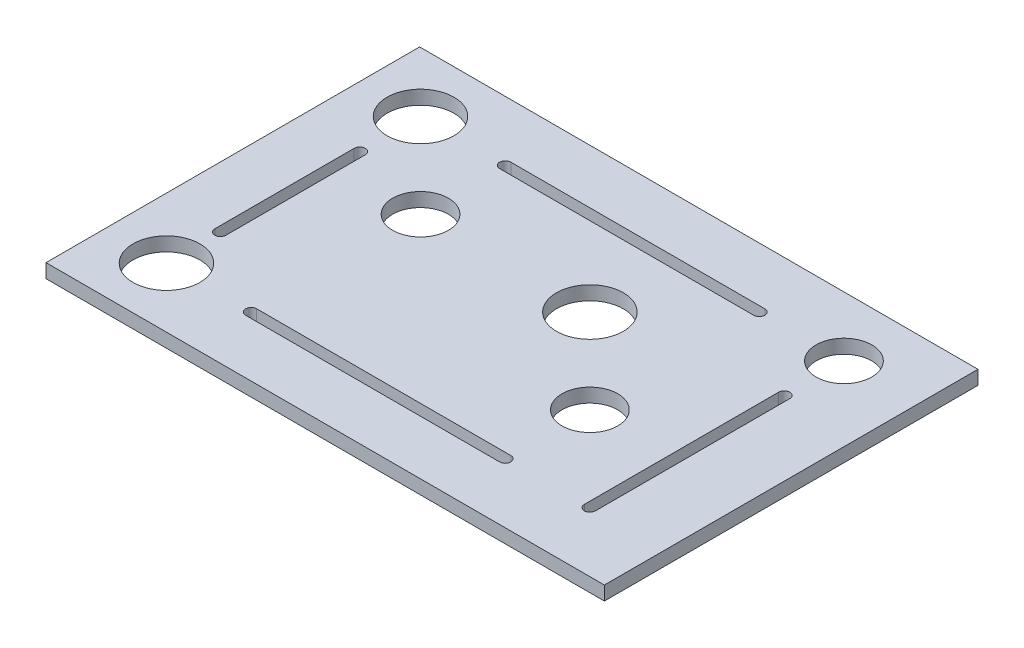
SolidWorks part; units mm, degrees
ref_plane "Front Plane" through (0, 0, 0) normal (0, 0, 1) x (1, 0, 0)
ref_plane "Top Plane" through (0, 0, 0) normal (0, 1, 0) x (1, 0, 0)
ref_plane "Right Plane" through (0, 0, 0) normal (1, 0, 0) x (0, 0, -1)
sketch "Sketch1" plane through (0, 0, 0) normal (0, 1, 0) x (1, 0, 0)
  line L1 (0, 0) -> (-127.25, 0)
  line L2 (0, 0) -> (0, 85.15)
  line L3 (0, 85.15) -> (-127.25, 85.15)
  line L4 (-127.25, 0) -> (-127.25, 85.15)
  dimension "D1" = 85.15
  dimension "D2" = 127.25
extrude "Boss-Extrude1" add sketch "Sketch1" along normal blind 3.175 contours L4 L3 L2 L1
sketch "Sketch2" plane through (0, 3.175, 0) normal (0, 1, 0) x (1, 0, 0)
  circle A0 centre (-16.925, 71.525) radius 6.35
  dimension "D1" = 12.7
extrude "Cut-Extrude1" cut sketch "Sketch2" against normal through all
sketch "Sketch3" plane through (0, 0, 0) normal (0, -1, 0) x (-1, 0, 0)
  circle A0 centre (113.425, 71.525) radius 7.62
  circle A1 centre (113.425, 13.625) radius 7.62
  circle A2 centre (94.125, 52.225) radius 6.35
  circle A3 centre (55.525, 52.225) radius 7.62
  circle A4 centre (36.225, 32.925) radius 6.35
  dimension "D1" = 12.7
  dimension "D2" = 12.7
  dimension "D3" = 15.24
  dimension "D4" = 15.24
  dimension "D5" = 15.24
extrude "Cut-Extrude2" cut sketch "Sketch3" against normal through all
sketch "Sketch4" plane through (0, 3.175, 0) normal (0, 1, 0) x (1, 0, 0)
  line L0 (-16.925, 13.625) -> (-16.925, 57.914) construction
  line L1 (-18.195, 13.625) -> (-18.195, 57.914)
  line L2 (-15.655, 13.625) -> (-15.655, 57.914)
  line L3 (-36.225, 71.525) -> (-94.125, 71.525) construction
  line L4 (-36.225, 70.255) -> (-94.125, 70.255)
  line L5 (-36.225, 72.795) -> (-94.125, 72.795)
  line L6 (-63.625, 0) -> (-63.625, 85.15) construction
  line L7 (0, 0) -> (-127.25, 0) construction
  line L8 (0, 85.15) -> (-127.25, 85.15) construction
  line L9 (0, 42.575) -> (-127.25, 42.575) construction
  line L10 (0, 0) -> (0, 85.15) construction
  line L11 (-127.25, 0) -> (-127.25, 85.15) construction
  line L12 (-113.425, 25.9053) -> (-113.425, 57.6832) construction
  line L13 (-114.695, 25.9053) -> (-114.695, 57.6832)
  line L14 (-112.155, 25.9053) -> (-112.155, 57.6832)
  line L15 (-113.425, 13.625) -> (-113.425, 28.9419) construction
  line L16 (-113.425, 71.525) -> (-113.425, 57.6832) construction
  line L17 (-16.925, 52.225) -> (-16.925, 13.625) construction
  line L18 (-16.925, 71.525) -> (-16.925, 57.914) construction
  line L19 (-36.225, 13.625) -> (-94.125, 13.625) construction
  line L20 (-36.225, 14.895) -> (-94.125, 14.895)
  line L21 (-36.225, 12.355) -> (-94.125, 12.355)
  arc A0 (-18.195, 13.625) -> (-15.655, 13.625) centre (-16.925, 13.625) ccw
  arc A1 (-15.655, 57.914) -> (-18.195, 57.914) centre (-16.925, 57.914) ccw
  arc A2 (-36.225, 70.255) -> (-36.225, 72.795) centre (-36.225, 71.525) ccw
  arc A3 (-94.125, 72.795) -> (-94.125, 70.255) centre (-94.125, 71.525) ccw
  arc A4 (-114.695, 25.9053) -> (-112.155, 25.9053) centre (-113.425, 25.9053) ccw
  arc A5 (-112.155, 57.6832) -> (-114.695, 57.6832) centre (-113.425, 57.6832) ccw
  arc A6 (-36.225, 14.895) -> (-36.225, 12.355) centre (-36.225, 13.625) cw
  arc A7 (-94.125, 12.355) -> (-94.125, 14.895) centre (-94.125, 13.625) cw
  point P4 (-16.925, 35.7695)
  point P9 (-65.175, 71.525)
  point P32 (-113.425, 41.7942)
  point P47 (-65.175, 13.625)
  dimension "D1" = 2.54
  dimension "D2" = 2.54
  dimension "D3" = 2.54
extrude "Cut-Extrude3" cut sketch "Sketch4" against normal through all
